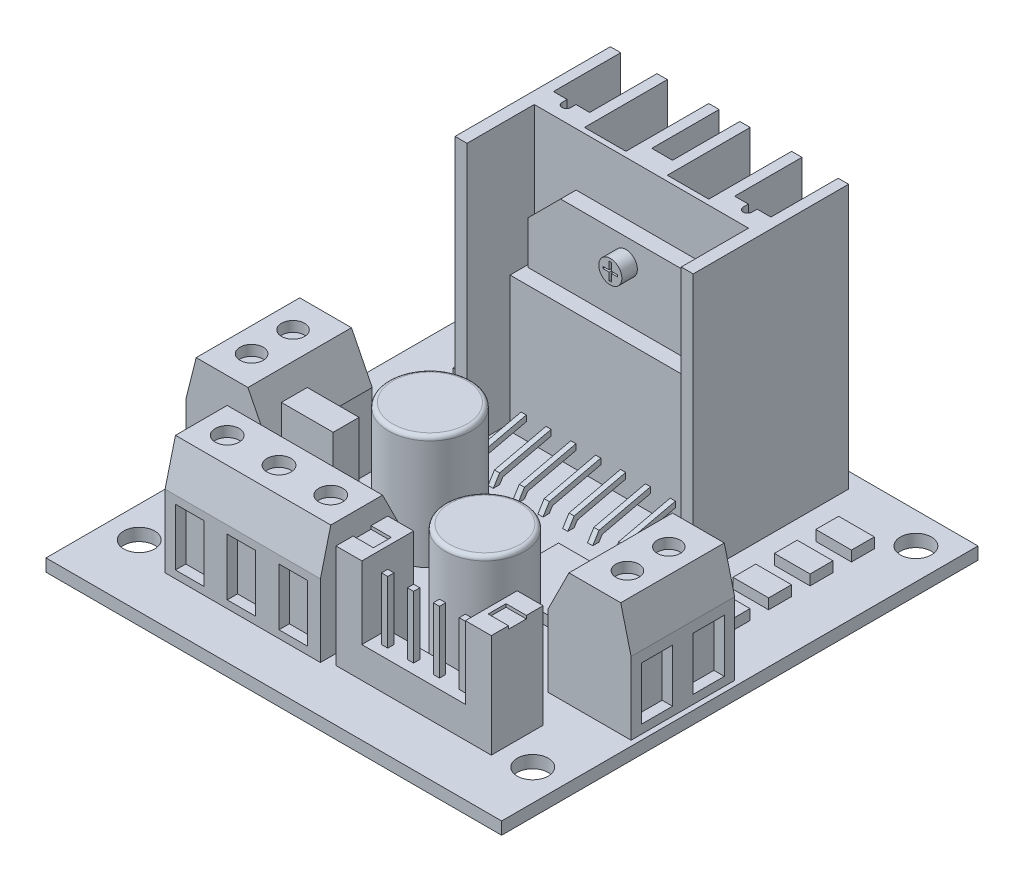
SolidWorks part; units mm, degrees
ref_plane "Alzado" through (0, 0, 0) normal (0, 0, 1) x (1, 0, 0)
ref_plane "Planta" through (0, 0, 0) normal (0, 1, 0) x (1, 0, 0)
ref_plane "Vista lateral" through (0, 0, 0) normal (1, 0, 0) x (0, 0, -1)
sketch "Croquis1" plane through (0, 0, 0) normal (0, 1, 0) x (1, 0, 0)
  line L0 (0, 0) -> (0, -13.9833) construction
  line L1 (-22, 23) -> (22, 23)
  line L2 (-22, 23) -> (-22, -23)
  line L3 (-22, -23) -> (22, -23)
  line L4 (22, 23) -> (22, -23)
  line L5 (-22, 23) -> (22, -23) construction
  line L6 (-22, -23) -> (22, 23) construction
  circle A0 centre (-19, 20) radius 1.5
  circle A1 centre (-19, -17) radius 1.5
  circle A2 centre (19, -17) radius 1.5
  circle A3 centre (19, 20) radius 1.5
  point P0 (0, 0)
  dimension "D3" = 3
  dimension "D5" = 6
  dimension "D1" = 44
  dimension "D2" = 46
  dimension "D4" = 3
  dimension "D6" = 3
extrude "Saliente-Extruir1" add sketch "Croquis1" along normal blind 1.2
sketch "Croquis2" plane through (0, 1.2, 0) normal (0, 1, 0) x (1, 0, 0)
  line L0 (-11, 21.5) -> (-11, 15)
  line L1 (-12, 21.5) -> (-11, 21.5)
  line L2 (-12, 21.5) -> (-12, 6.5)
  line L3 (-12, 6.5) -> (-10.8432, 6.5)
  line L4 (11, 21.5) -> (11, 6.5)
  line L5 (-12, 21.5) -> (11, 6.5) construction
  line L6 (-12, 6.5) -> (11, 21.5) construction
  line L7 (-7.5, 21.5) -> (-7.5, 15)
  line L8 (-6.5, 21.5) -> (-6.5, 13.5)
  line L9 (-2.5, 21.5) -> (-2.5, 13.5)
  line L10 (-1.5, 21.5) -> (-1.5, 15)
  line L11 (-11, 15) -> (-9.6769, 15)
  line L12 (-6.5, 13.5) -> (-2.5, 13.5)
  line L13 (9.8432, 6.5) -> (11, 6.5)
  line L14 (-7.5, 21.5) -> (-7.5, 11.9163) construction
  line L15 (-6.5, 15) -> (-6.0594, 15)
  line L16 (-6.5, 21.5) -> (-6.5, 11.9163) construction
  line L17 (-8.8231, 15) -> (-8.8231, 14.5062)
  line L18 (-9.6769, 15) -> (-9.6769, 14.5062)
  line L19 (-8.8231, 15) -> (-7.5, 15)
  line L20 (-1.5, 21.5) -> (-1.5, 11.9163) construction
  line L21 (-2.5, 21.5) -> (-2.5, 11.9163) construction
  line L22 (-0.5, 14) -> (-0.5, 10.3568) construction
  line L23 (0.5, 21.5) -> (0.5, 15)
  line L24 (1.5, 21.5) -> (1.5, 13.5)
  line L25 (5.5, 13.5) -> (1.5, 13.5)
  line L26 (5.5, 21.5) -> (5.5, 13.5)
  line L27 (8.6769, 15) -> (8.6769, 14.5062)
  line L28 (7.8231, 15) -> (7.8231, 14.5062)
  line L29 (7.8231, 15) -> (6.5, 15)
  line L30 (10, 15) -> (8.6769, 15)
  line L31 (6.5, 21.5) -> (6.5, 15)
  line L32 (10, 21.5) -> (10, 15)
  line L33 (-0.5, 6.5) -> (-0.5, 10) construction
  line L34 (0.5, 15) -> (-1.5, 15)
  line L35 (-10.8432, 7.0064) -> (-10.8432, 6.5)
  line L36 (-10.8432, 12.9936) -> (9.8432, 12.9936)
  line L37 (-10.8432, 12.9936) -> (-10.8432, 7.0064)
  line L39 (9.8432, 12.9936) -> (9.8432, 7.0064)
  line L40 (-10.8432, 12.9936) -> (9.8432, 7.0064) construction
  line L41 (-10.8432, 7.0064) -> (9.8432, 12.9936) construction
  line L42 (9.8432, 7.0064) -> (9.8432, 6.5)
  line L43 (-7.5, 21.5) -> (-6.5, 21.5)
  line L44 (-2.5, 21.5) -> (-1.5, 21.5)
  line L45 (5.5, 21.5) -> (6.5, 21.5)
  line L46 (0.5, 21.5) -> (1.5, 21.5)
  line L47 (10, 21.5) -> (11, 21.5)
  line L48 (22, -23) -> (22, 23) construction
  line L49 (22, 23) -> (-22, 23) construction
  arc A1 (-9.6769, 14.5062) -> (-8.8231, 14.5062) centre (-9.25, 14.5062) ccw
  arc A2 (8.6769, 14.5062) -> (7.8231, 14.5062) centre (8.25, 14.5062) cw
  point P0 (-0.5, 14)
  point P24 (-5.9103, 15.0438)
  dimension "D1" = 15
  dimension "D2" = 23
  dimension "D3" = 1
  dimension "D4" = 3.5
  dimension "D8" = 6.5
  dimension "D9" = 8
  dimension "D10" = 3.5
  dimension "D11" = 11
  dimension "D12" = 1.5
  dimension "D5" = 1
  dimension "D6" = 4
  dimension "D7" = 1
extrude "Saliente-Extruir2" add sketch "Croquis2" along normal blind 25.5 contours L27 A2 L28 L29 L31 L45 L26 L25 L24 L46 L23 L34 L10 L44 L9 L12 L8 L43 L7 L19 L17 A1 L18 L11 L0 L1 L2 L3 L35 L37 L36 L39 L42 L13 L4 L47 L32 L30
sketch "Croquis3" plane through (0, 0, -12.9936) normal (0, 0, 1) x (1, 0, 0)
  line L0 (-10.8432, 7.7335) -> (9.8432, 7.7335)
  line L1 (-10.8432, 26.7) -> (-10.8432, 1.2) construction
  line L2 (9.8432, 26.7) -> (9.8432, 1.2) construction
  line L3 (-10.8432, 1.2) -> (9.8432, 1.2) construction
  line L4 (-10.1827, 14.267) -> (9.1827, 14.267)
  line L5 (-10.1827, 14.267) -> (-10.1827, 1.2)
  line L6 (-10.1827, 1.2) -> (9.1827, 1.2)
  line L7 (9.1827, 14.267) -> (9.1827, 1.2)
  line L8 (-10.1827, 14.267) -> (9.1827, 1.2) construction
  line L9 (-10.1827, 1.2) -> (9.1827, 14.267) construction
  line L10 (-9.9371, 14.267) -> (-9.9371, 18.4293)
  line L11 (-9.9371, 18.4293) -> (-6.8014, 21.565)
  line L12 (-6.8014, 21.565) -> (5.8014, 21.565)
  line L13 (-0.5, 21.565) -> (-0.5, 14.267) construction
  line L14 (8.9371, 14.267) -> (8.9371, 18.4293)
  line L15 (8.9371, 18.4293) -> (5.8014, 21.565)
  point P6 (-0.5, 7.7335)
  line M9 (-10.8432, 1.2) -> (9.8432, 1.2)
extrude "Saliente-Extruir3" add sketch "Croquis3" along normal blind 1.5 contours L14 L15 L12 L11 L10 L4 | L7 L4 L5 L0 | L7 L0 L5 M9
sketch "Croquis4" plane through (0, 0, -11.4936) normal (0, 0, 1) x (1, 0, 0)
  line L0 (-9.9371, 14.267) -> (8.9371, 14.267)
  line L2 (-0.6058, 20.2107) -> (-0.3942, 20.2107)
  line L3 (-0.6058, 20.2107) -> (-0.6058, 18.5641)
  line L4 (-0.6058, 18.5641) -> (-0.3942, 18.5641)
  line L5 (-0.3942, 20.2107) -> (-0.3942, 18.5641)
  line L6 (-0.6058, 20.2107) -> (-0.3942, 18.5641) construction
  line L7 (-0.6058, 18.5641) -> (-0.3942, 20.2107) construction
  line L8 (-1.1956, 19.4768) -> (0.1956, 19.4768)
  line L9 (-1.1956, 19.4768) -> (-1.1956, 19.298)
  line L10 (8.9371, 14.267) -> (8.9371, 18.4293)
  line L11 (8.9371, 18.4293) -> (5.8014, 21.565)
  line L12 (5.8014, 21.565) -> (-6.8014, 21.565)
  line L13 (-6.8014, 21.565) -> (-9.9371, 18.4293)
  line L14 (-9.9371, 18.4293) -> (-9.9371, 14.267)
  line L15 (-9.9371, 14.267) -> (-10.1827, 14.267)
  line L16 (-10.1827, 14.267) -> (-10.1827, 1.2)
  line L17 (-10.1827, 1.2) -> (9.1827, 1.2)
  line L18 (9.1827, 1.2) -> (9.1827, 14.267)
  line L19 (9.1827, 14.267) -> (8.9371, 14.267)
  line L25 (-9.9371, 14.267) -> (-10.1827, 14.267)
  line L26 (-10.1827, 14.267) -> (-10.1827, 1.2)
  line L27 (-10.1827, 1.2) -> (9.1827, 1.2)
  line L28 (9.1827, 1.2) -> (9.1827, 14.267)
  line L29 (9.1827, 14.267) -> (8.9371, 14.267)
  line L30 (-1.1956, 19.298) -> (0.1956, 19.298)
  line L31 (0.1956, 19.4768) -> (0.1956, 19.298)
  line L32 (-1.1956, 19.4768) -> (0.1956, 19.298) construction
  line L33 (-1.1956, 19.298) -> (0.1956, 19.4768) construction
  circle A0 centre (-0.5, 19.3874) radius 1.1143
  line M16 (-9.9371, 14.267) -> (-10.1827, 14.267)
  line M17 (-10.1827, 14.267) -> (-10.1827, 1.2)
  line M18 (-10.1827, 1.2) -> (9.1827, 1.2)
  line M19 (9.1827, 1.2) -> (9.1827, 14.267)
  line M20 (9.1827, 14.267) -> (8.9371, 14.267)
  dimension "D1" = 0
extrude "Saliente-Extruir4" add sketch "Croquis4" along normal blind 1.5 contours L0 M16 M17 M18 M19 M20 | A0 L8 L31 L30 L5 L4 L3 L9 L2
ref_plane "Plano1" through (7.9327, 0, 0) normal (1, 0, 0) x (0, 0, -1)
sketch "Croquis6" plane through (7.9327, 0, 0) normal (1, 0, 0) x (0, 0, -1)
  line L0 (9.9936, 3.3424) -> (5.0225, 2.1849)
  line L1 (9.9936, 14.267) -> (9.9936, 1.2) construction
  line L2 (5.0225, 2.1849) -> (4.4097, 1.2)
  line L3 (23, 1.2) -> (-23, 1.2) construction
  line L4 (4.4097, 1.2) -> (5.0225, 1.2)
  line L5 (5.0225, 1.2) -> (5.329, 1.6924)
  line L6 (5.329, 1.6924) -> (9.9936, 2.7786)
  line L7 (9.9936, 2.7786) -> (9.9936, 3.3424)
extrude "Saliente-Extruir5" add sketch "Croquis6" along normal blind 0.25 and the other way blind 0.25
pattern_linear "MatrizL1" count 8 spacing 2.4 along (-1, 0, 0) of "Saliente-Extruir5"
sketch "Croquis7" plane through (0, 1.2, 0) normal (0, 1, 0) x (1, 0, 0)
  line L0 (-17.2352, 13.7523) -> (-13.7882, 11.5462) construction
  line L1 (-17.2352, 17.7523) -> (-13.7882, 17.7523)
  line L2 (-17.2352, 17.7523) -> (-17.2352, 15.5462)
  line L3 (-17.2352, 15.5462) -> (-13.7882, 15.5462)
  line L4 (-13.7882, 17.7523) -> (-13.7882, 15.5462)
  line L5 (-17.2352, 17.7523) -> (-13.7882, 15.5462) construction
  line L6 (-17.2352, 15.5462) -> (-13.7882, 17.7523) construction
  line L7 (-17.2352, 11.5462) -> (-13.7882, 13.7523) construction
  line L8 (-17.2352, 13.7523) -> (-17.2352, 11.5462)
  line L9 (-17.2352, 13.7523) -> (-13.7882, 13.7523)
  line L10 (-13.7882, 13.7523) -> (-13.7882, 11.5462)
  line L11 (-17.2352, 11.5462) -> (-13.7882, 11.5462)
  line L12 (-17.2352, 9.7523) -> (-13.7882, 7.5462) construction
  line L13 (-17.2352, 7.5462) -> (-13.7882, 9.7523) construction
  line L14 (-17.2352, 9.7523) -> (-17.2352, 7.5462)
  line L15 (-17.2352, 9.7523) -> (-13.7882, 9.7523)
  line L16 (-13.7882, 9.7523) -> (-13.7882, 7.5462)
  line L17 (-17.2352, 7.5462) -> (-13.7882, 7.5462)
  line L18 (-17.2352, 5.7523) -> (-13.7882, 3.5462) construction
  line L19 (-17.2352, 3.5462) -> (-13.7882, 5.7523) construction
  line L20 (-17.2352, 5.7523) -> (-17.2352, 3.5462)
  line L21 (-17.2352, 5.7523) -> (-13.7882, 5.7523)
  line L22 (-13.7882, 5.7523) -> (-13.7882, 3.5462)
  line L23 (-17.2352, 3.5462) -> (-13.7882, 3.5462)
  line L24 (0, 0) -> (0, -5.3512) construction
  line L25 (17.2352, 3.5462) -> (13.7882, 5.7523) construction
  line L26 (17.2352, 5.7523) -> (13.7882, 3.5462) construction
  line L27 (17.2352, 7.5462) -> (13.7882, 9.7523) construction
  line L28 (17.2352, 9.7523) -> (13.7882, 7.5462) construction
  line L29 (17.2352, 11.5462) -> (13.7882, 13.7523) construction
  line L30 (17.2352, 15.5462) -> (13.7882, 17.7523) construction
  line L31 (17.2352, 17.7523) -> (13.7882, 15.5462) construction
  line L32 (17.2352, 13.7523) -> (13.7882, 11.5462) construction
  line L33 (17.2352, 3.5462) -> (13.7882, 3.5462)
  line L34 (13.7882, 5.7523) -> (13.7882, 3.5462)
  line L35 (17.2352, 5.7523) -> (13.7882, 5.7523)
  line L36 (17.2352, 5.7523) -> (17.2352, 3.5462)
  line L37 (17.2352, 7.5462) -> (13.7882, 7.5462)
  line L38 (13.7882, 9.7523) -> (13.7882, 7.5462)
  line L39 (17.2352, 9.7523) -> (13.7882, 9.7523)
  line L40 (17.2352, 9.7523) -> (17.2352, 7.5462)
  line L41 (17.2352, 11.5462) -> (13.7882, 11.5462)
  line L42 (13.7882, 13.7523) -> (13.7882, 11.5462)
  line L43 (17.2352, 13.7523) -> (13.7882, 13.7523)
  line L44 (17.2352, 13.7523) -> (17.2352, 11.5462)
  line L45 (13.7882, 17.7523) -> (13.7882, 15.5462)
  line L46 (17.2352, 15.5462) -> (13.7882, 15.5462)
  line L47 (17.2352, 17.7523) -> (17.2352, 15.5462)
  line L48 (17.2352, 17.7523) -> (13.7882, 17.7523)
  line L50 (2.5023, 1.9928) -> (8.2995, 1.9928)
  line L51 (2.5023, 1.9928) -> (2.5023, -4.5399)
  line L52 (2.5023, -4.5399) -> (8.2995, -4.5399)
  line L53 (8.2995, 1.9928) -> (8.2995, -4.5399)
  line L54 (2.5023, 1.9928) -> (8.2995, -4.5399) construction
  line L55 (2.5023, -4.5399) -> (8.2995, 1.9928) construction
  point P0 (-15.5117, 16.6492)
  point P7 (-15.5117, 12.6492)
  point P12 (-15.5117, 8.6492)
  point P17 (-15.5117, 4.6492)
  point P39 (15.5117, 4.6492)
  point P40 (15.5117, 8.6492)
  point P41 (15.5117, 12.6492)
  point P42 (15.5117, 16.6492)
  point P43 (5.4009, -1.2736)
  dimension "D1" = 4
extrude "Saliente-Extruir6" add sketch "Croquis7" along normal blind 1
sketch "Croquis8" plane through (0, 1.2, 0) normal (0, 1, 0) x (1, 0, 0)
  line L0 (-22, 23) -> (-22, -23) construction
  line L1 (-21.5, 0) -> (-13.5, 0)
  line L2 (-21.5, 0) -> (-21.5, -10)
  line L3 (-21.5, -10) -> (-13.5, -10)
  line L4 (-13.5, 0) -> (-13.5, -10)
  line L5 (-21.5, 0) -> (-13.5, -10) construction
  line L6 (-21.5, -10) -> (-13.5, 0) construction
  line L7 (-22, -23) -> (22, -23) construction
  point P0 (-17.5, -5)
  dimension "D1" = 10
  dimension "D2" = 8
  dimension "D3" = 0.5
  dimension "D4" = 13
extrude "Saliente-Extruir7" add sketch "Croquis8" along normal blind 11
sketch "Croquis9" plane through (0, 0, 10) normal (0, 0, 1) x (1, 0, 0)
  line L0 (-21.5, 8.2) -> (-20.5, 12.2)
  line L1 (-15.5, 12.2) -> (-13.5, 8.2)
  line L2 (-20.5, 12.2) -> (-21.5, 12.2)
  line L4 (-21.5, 1.2) -> (-13.5, 1.2)
  line L5 (-13.5, 1.2) -> (-13.5, 12.2)
  line L6 (-13.5, 12.2) -> (-21.5, 12.2)
  line L7 (-21.5, 12.2) -> (-21.5, 1.2)
  line L9 (-13.5, 8.2) -> (-13.5, 12.2)
  line L10 (-13.5, 12.2) -> (-15.5, 12.2)
  line L11 (-21.5, 12.2) -> (-21.5, 8.2)
  dimension "D2" = 4
  dimension "D3" = 5
  dimension "D4" = 1
  dimension "D5" = 4
  dimension "D1" = 0
extrude "Cortar-Extruir1" cut sketch "Croquis9" against normal blind 11
sketch "Croquis10" plane through (0, 12.2, 0) normal (0, 1, 0) x (1, 0, 0)
  line L0 (-15.5, 0) -> (-20.5, 0) construction
  circle A0 centre (-18.1447, -3) radius 1.111
  circle A3 centre (-18.1447, -7) radius 1.111
  dimension "D1" = 3
  dimension "D2" = 2
extrude "Cortar-Extruir2" cut sketch "Croquis10" against normal blind 1
sketch "Croquis11" plane through (-21.5, 0, 0) normal (-1, 0, 0) x (0, 0, 1)
  line L0 (0, 8.2) -> (0, 1.2) construction
  line L1 (1, 7.1567) -> (4, 7.1567)
  line L2 (1, 7.1567) -> (1, 2.0425)
  line L3 (1, 2.0425) -> (4, 2.0425)
  line L4 (4, 7.1567) -> (4, 2.0425)
  line L5 (1, 7.1567) -> (4, 2.0425) construction
  line L6 (1, 2.0425) -> (4, 7.1567) construction
  line L7 (6, 7.1567) -> (6, 2.0425)
  line L8 (6, 7.1567) -> (9, 7.1567)
  line L9 (9, 7.1567) -> (9, 2.0425)
  line L10 (6, 2.0425) -> (9, 2.0425)
  point P0 (2.5, 4.5996)
  dimension "D1" = 1
  dimension "D2" = 3
  dimension "D3" = 2
extrude "Cortar-Extruir3" cut sketch "Croquis11" against normal blind 1
mirror "Simetría1" about plane through (0, 0, 0) normal (1, 0, 0) of "Saliente-Extruir7", "Cortar-Extruir1", "Cortar-Extruir2", "Cortar-Extruir3"
sketch "Croquis12" plane through (0, 1.2, 0) normal (0, 1, 0) x (1, 0, 0)
  line L0 (-22, -23) -> (22, -23) construction
  line L1 (-15, -10.5) -> (0, -10.5)
  line L2 (-15, -10.5) -> (-15, -18.5)
  line L3 (-15, -18.5) -> (0, -18.5)
  line L4 (0, -10.5) -> (0, -18.5)
  line L5 (-15, -10.5) -> (0, -18.5) construction
  line L6 (-15, -18.5) -> (0, -10.5) construction
  line L7 (-22, 23) -> (-22, -23) construction
  point P0 (-7.5, -14.5)
  dimension "D1" = 15
  dimension "D2" = 8
  dimension "D3" = 4.5
  dimension "D4" = 7
extrude "Saliente-Extruir8" add sketch "Croquis12" along normal blind 11
sketch "Croquis13" plane through (0, 0, 0) normal (1, 0, 0) x (0, 0, -1)
  line L0 (-18.5, 8.2) -> (-17.5, 12.2)
  line L1 (-12.5, 12.2) -> (-10.5, 8.2)
  line L3 (-17.5, 12.2) -> (-18.5, 12.2)
  line L4 (-18.5, 1.2) -> (-10.5, 1.2)
  line L5 (-10.5, 1.2) -> (-10.5, 12.2)
  line L6 (-10.5, 12.2) -> (-18.5, 12.2)
  line L7 (-18.5, 12.2) -> (-18.5, 1.2)
  line L9 (-10.5, 8.2) -> (-10.5, 12.2)
  line L10 (-10.5, 12.2) -> (-12.5, 12.2)
  line L11 (-18.5, 12.2) -> (-18.5, 8.2)
  dimension "D2" = 4
  dimension "D3" = 4
  dimension "D4" = 5
  dimension "D5" = 1
  dimension "D1" = 0
extrude "Cortar-Extruir4" cut sketch "Croquis13" against normal blind 15
sketch "Croquis14" plane through (0, 12.2, 0) normal (0, 1, 0) x (1, 0, 0)
  line L0 (-15, -12.5) -> (-15, -17.5) construction
  line L1 (-15, -12.5) -> (0, -12.5) construction
  circle A0 centre (-12.5, -15) radius 1.1533
  circle A1 centre (-7.5, -15) radius 1.1533
  circle A2 centre (-2.5, -15) radius 1.1533
  dimension "D1" = 2.5
  dimension "D3" = 2.5
  dimension "D2" = 3
extrude "Cortar-Extruir5" cut sketch "Croquis14" against normal blind 1
sketch "Croquis15" plane through (0, 0, 18.5) normal (0, 0, 1) x (1, 0, 0)
  line L0 (-15, 8.2) -> (-15, 1.2) construction
  line L1 (-14, 7.4419) -> (-11.2484, 7.4419)
  line L2 (-14, 7.4419) -> (-14, 1.9387)
  line L3 (-14, 1.9387) -> (-11.2484, 1.9387)
  line L4 (-11.2484, 7.4419) -> (-11.2484, 1.9387)
  line L5 (-14, 7.4419) -> (-11.2484, 1.9387) construction
  line L6 (-14, 1.9387) -> (-11.2484, 7.4419) construction
  line L7 (-9, 7.4419) -> (-9, 1.9387)
  line L8 (-9, 7.4419) -> (-6.2484, 7.4419)
  line L9 (-6.2484, 7.4419) -> (-6.2484, 1.9387)
  line L10 (-9, 1.9387) -> (-6.2484, 1.9387)
  line L11 (-4, 7.4419) -> (-4, 1.9387)
  line L12 (-4, 7.4419) -> (-1.2484, 7.4419)
  line L13 (-1.2484, 7.4419) -> (-1.2484, 1.9387)
  line L14 (-4, 1.9387) -> (-1.2484, 1.9387)
  point P0 (-12.6242, 4.6903)
  dimension "D1" = 1
  dimension "D2" = 3
extrude "Cortar-Extruir6" cut sketch "Croquis15" against normal blind 1
sketch "Croquis16" plane through (0, 1.2, 0) normal (0, 1, 0) x (1, 0, 0)
  line L0 (-22, -23) -> (22, -23) construction
  line L1 (1, -15.5) -> (16, -15.5)
  line L2 (1, -15.5) -> (1, -18)
  line L3 (1, -18) -> (16, -18)
  line L4 (16, -15.5) -> (16, -18)
  line L5 (1, -15.5) -> (16, -18) construction
  line L6 (1, -18) -> (16, -15.5) construction
  line L7 (22, -23) -> (22, 23) construction
  point P0 (8.5, -16.75)
  point P7 (16, -16.75)
  dimension "D1" = 2.5
  dimension "D2" = 15
  dimension "D3" = 5
  dimension "D4" = 6
extrude "Saliente-Extruir9" add sketch "Croquis16" along normal blind 3
sketch "Croquis17" plane through (0, 4.2, 0) normal (0, 1, 0) x (1, 0, 0)
  line L0 (1, -15.5) -> (1, -18) construction
  line L1 (1.95, -16.45) -> (2.55, -16.45)
  line L2 (1.95, -16.45) -> (1.95, -17.05)
  line L3 (1.95, -17.05) -> (2.55, -17.05)
  line L4 (2.55, -16.45) -> (2.55, -17.05)
  line L5 (1.95, -16.45) -> (2.55, -17.05) construction
  line L6 (1.95, -17.05) -> (2.55, -16.45) construction
  line L9 (1, -18) -> (16, -18) construction
  line L10 (4.45, -16.45) -> (4.45, -17.05)
  line L11 (4.45, -16.45) -> (5.05, -16.45)
  line L12 (5.05, -16.45) -> (5.05, -17.05)
  line L13 (4.45, -17.05) -> (5.05, -17.05)
  line L14 (6.95, -16.45) -> (6.95, -17.05)
  line L15 (6.95, -16.45) -> (7.55, -16.45)
  line L16 (7.55, -16.45) -> (7.55, -17.05)
  line L17 (6.95, -17.05) -> (7.55, -17.05)
  line L18 (9.45, -16.45) -> (9.45, -17.05)
  line L19 (9.45, -16.45) -> (10.05, -16.45)
  line L20 (10.05, -16.45) -> (10.05, -17.05)
  line L21 (9.45, -17.05) -> (10.05, -17.05)
  line L22 (11.95, -16.45) -> (11.95, -17.05)
  line L23 (11.95, -16.45) -> (12.55, -16.45)
  line L24 (12.55, -16.45) -> (12.55, -17.05)
  line L25 (11.95, -17.05) -> (12.55, -17.05)
  line L26 (14.45, -16.45) -> (14.45, -17.05)
  line L27 (14.45, -16.45) -> (15.05, -16.45)
  line L28 (15.05, -16.45) -> (15.05, -17.05)
  line L29 (14.45, -17.05) -> (15.05, -17.05)
  point P0 (2.25, -16.75)
  dimension "D1" = 0.6
  dimension "D2" = 0.6
  dimension "D3" = 1.25
  dimension "D4" = 1.25
  dimension "D5" = 6
extrude "Saliente-Extruir10" add sketch "Croquis17" along normal blind 6
sketch "Croquis18" plane through (0, 4.2, 0) normal (0, 1, 0) x (1, 0, 0)
  line L0 (8.5, -15.5) -> (8.5, -12.7352) construction
  line L2 (16, -15.5) -> (1, -15.5) construction
  line L3 (1, -18) -> (3.5, -18)
  line L4 (1, -18) -> (1, -13)
  line L5 (1, -13) -> (3.5, -13)
  line L6 (3.5, -18) -> (3.5, -13)
  line L7 (16, -13) -> (13.5, -13)
  line L8 (13.5, -18) -> (13.5, -13)
  line L9 (16, -18) -> (13.5, -18)
  line L10 (16, -18) -> (16, -13)
  dimension "D1" = 2.5
  dimension "D2" = 5
extrude "Saliente-Extruir11" add sketch "Croquis18" along normal blind 7 and the other way up to surface (4.2 mm away)
sketch "Croquis19" plane through (0, 11.2, 0) normal (0, 1, 0) x (1, 0, 0)
  line L0 (1, -13) -> (1, -18) construction
  line L1 (1, -14.6159) -> (2.9611, -14.6159)
  line L2 (1, -14.6159) -> (1, -16.3434)
  line L3 (1, -16.3434) -> (2.9611, -16.3434)
  line L4 (2.9611, -14.6159) -> (2.9611, -16.3434)
  line L5 (8.5, -15.5) -> (8.5, -12.6004) construction
  line L6 (13.5, -15.5) -> (3.5, -15.5) construction
  line L7 (16, -16.3434) -> (14.0389, -16.3434)
  line L8 (14.0389, -14.6159) -> (14.0389, -16.3434)
  line L9 (16, -14.6159) -> (14.0389, -14.6159)
  line L10 (16, -14.6159) -> (16, -16.3434)
extrude "Cortar-Extruir7" cut sketch "Croquis19" against normal blind 0.3
sketch "Croquis20" plane through (0, 1.2, 0) normal (0, 1, 0) x (1, 0, 0)
  line L1 (-12.6382, -7.132) -> (-7.6382, -7.132)
  line L2 (-12.6382, -7.132) -> (-12.6382, -9.632)
  line L3 (-12.6382, -9.632) -> (-7.6382, -9.632)
  line L4 (-7.6382, -7.132) -> (-7.6382, -9.632)
  line L5 (-12.6382, -7.132) -> (-7.6382, -9.632) construction
  line L6 (-12.6382, -9.632) -> (-7.6382, -7.132) construction
  circle A0 centre (-5.4601, -2.4646) radius 3.9913
  circle A1 centre (7.356, -9.9723) radius 3.8107
  point P4 (-10.1382, -8.382)
  dimension "D1" = 5
  dimension "D2" = 2.5
extrude "Saliente-Extruir12" add sketch "Croquis20" along normal blind 11
fillet "Redondeo1" radius 0.4 2 edges at (7.356, 12.2, 13.783) (-5.4601, 12.2, 6.4559)
